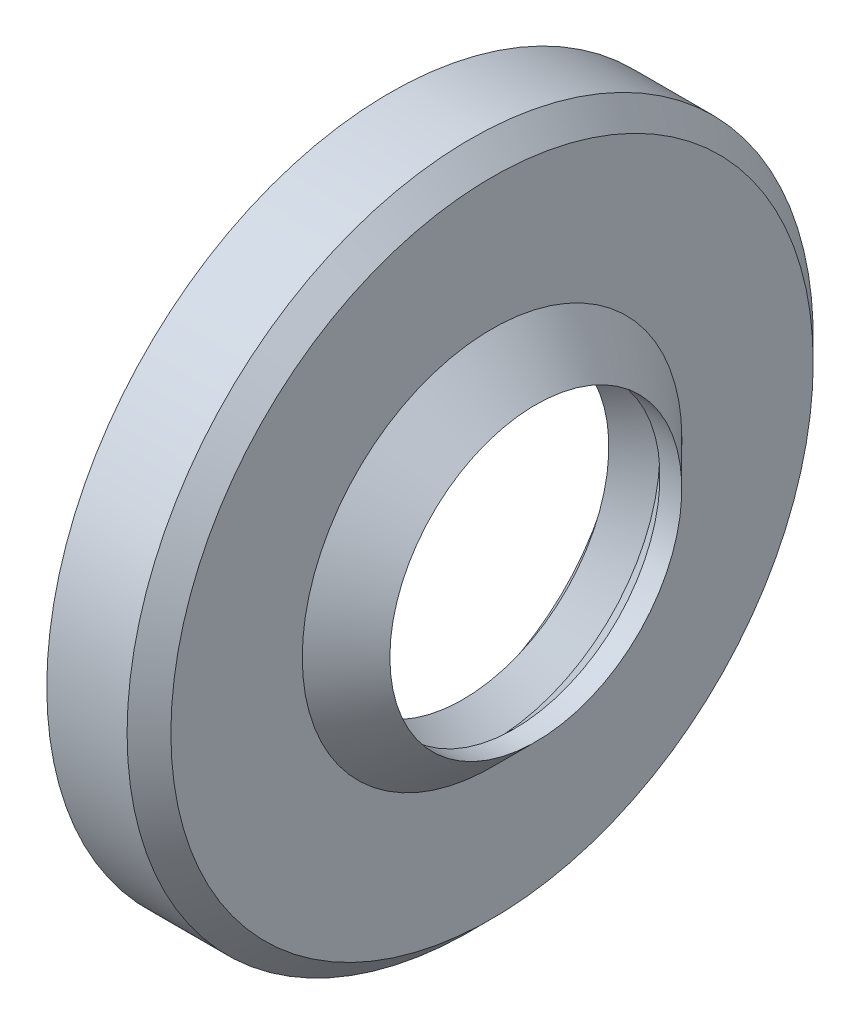
SolidWorks part; units mm, degrees
material "AISI 1020"
ref_plane "Спереди" through (0, 0, 0) normal (0, 0, 1) x (1, 0, 0)
ref_plane "Сверху" through (0, 0, 0) normal (0, 1, 0) x (1, 0, 0)
ref_plane "Справа" through (0, 0, 0) normal (1, 0, 0) x (0, 0, -1)
sketch "Эскиз1" plane through (0, 0, 0) normal (0, 0, 1) x (1, 0, 0)
  line L0 (-1000, 0) -> (49000, 0) construction
  line L1 (0, 22) -> (0, 23.5)
  line L2 (0, 23.5) -> (5.5, 23.5)
  line L3 (5.5, 23.5) -> (7, 22)
  line L4 (7, 22) -> (7, 13)
  line L5 (7, 13) -> (10, 10)
  line L6 (10, 10) -> (8.5, 10)
  line L7 (8.5, 10) -> (7, 11.5)
  line L8 (7, 11.5) -> (5, 10)
  line L9 (5, 10) -> (2.75, 13)
  line L10 (2.75, 13) -> (2.75, 14.5)
  line L11 (2.75, 14.5) -> (5.5, 14.5)
  line L12 (5.5, 14.5) -> (5.5, 22)
  line L14 (5.5, 22) -> (0, 22)
  line L15 (5.5, 22) -> (7, 22) construction
  point P5 (8.5222, 29.7724)
  point P7 (8, 8.6244)
  point P18 (15.3204, 24.7118)
  point P20 (8.7827, 20.1554)
  point P21 (13.5746, 10)
  point P22 (12.9415, 10)
  point P23 (8.7637, 23.5)
  point P24 (6.7668, 11.7332)
  point P25 (-1.6013, 10)
  point P26 (8, 20.1004)
  point P27 (8, 22.2054)
  point P28 (2.6649, 12.9802)
  point P29 (8, 11.0364)
  point P30 (8, 14.4802)
  point P31 (2.75, 22)
  point P32 (7.5952, 10.9048)
  point P33 (5.5, 14.273)
  point P34 (0, 0)
  point P35 (0, 0)
  dimension "D1" = 45
  dimension "D2" = 20
  dimension "D3" = 47
  dimension "D4" = 1.5
  dimension "D5" = 10
  dimension "D6" = 7
revolve "Повернуть1" add sketch "Эскиз1" angle 360 about L0
